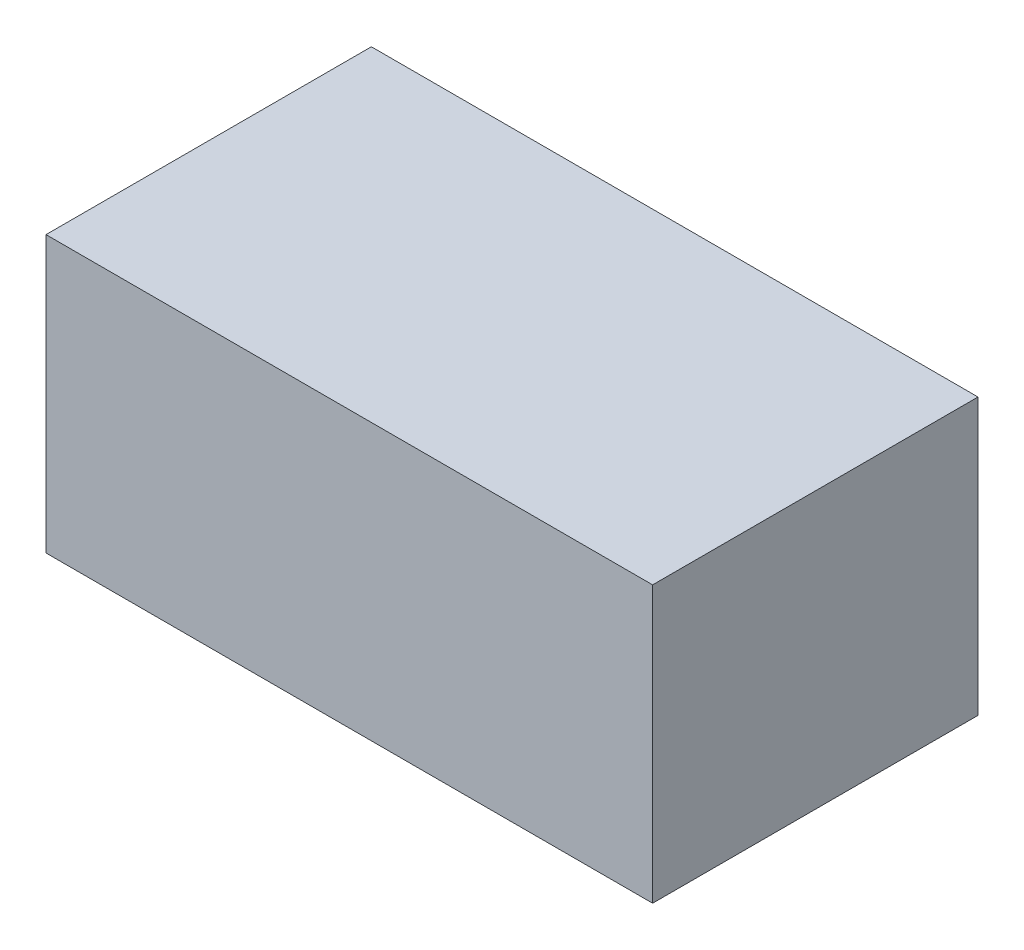
SolidWorks part; units mm, degrees
ref_plane "Front Plane" through (0, 0, 0) normal (0, 0, 1) x (1, 0, 0)
ref_plane "Top Plane" through (0, 0, 0) normal (0, 1, 0) x (1, 0, 0)
ref_plane "Right Plane" through (0, 0, 0) normal (1, 0, 0) x (0, 0, -1)
sketch "Sketch1" plane through (0, 0, 0) normal (0, 0, 1) x (1, 0, 0)
  line L1 (-139.7, -63.5) -> (139.7, -63.5)
  line L2 (-139.7, -63.5) -> (-139.7, 63.5)
  line L3 (-139.7, 63.5) -> (139.7, 63.5)
  line L4 (139.7, -63.5) -> (139.7, 63.5)
  line L5 (-139.7, -63.5) -> (139.7, 63.5) construction
  line L6 (-139.7, 63.5) -> (139.7, -63.5) construction
  point P0 (0, 0)
  dimension "D1" = 279.4
  dimension "D2" = 127
extrude "Extrude1" add sketch "Sketch1" along normal blind 149.86
